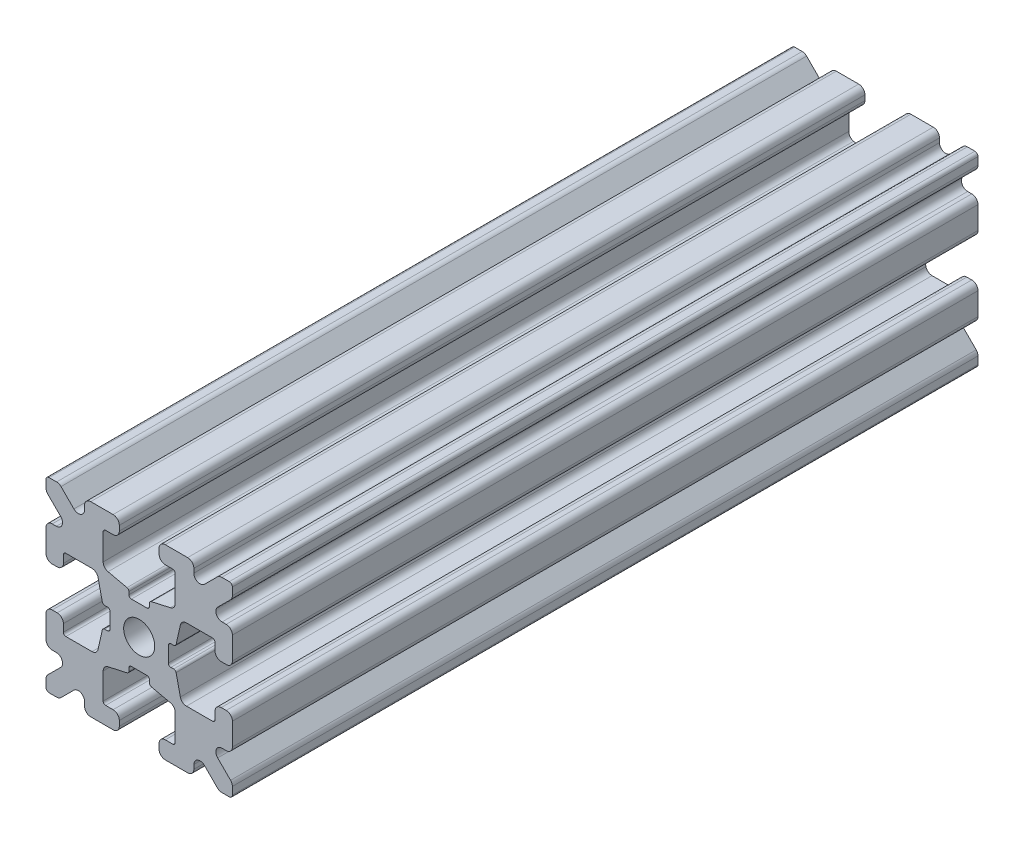
SolidWorks part; units mm, degrees
ref_plane "Front Plane" through (0, 0, 0) normal (0, 0, 1) x (1, 0, 0)
ref_plane "Top Plane" through (0, 0, 0) normal (0, 1, 0) x (1, 0, 0)
ref_plane "Right Plane" through (0, 0, 0) normal (1, 0, 0) x (0, 0, -1)
sketch "Profile" plane through (0, 0, 0) normal (0, 0, 1) x (1, 0, 0)
  line L0 (0.6255, -2.3471) -> (-0.6255, -2.3471)
  line L1 (-0.8255, -2.5471) -> (-0.8255, -2.7749)
  line L2 (-0.9818, -2.97) -> (-2.5094, -3.3124)
  line L3 (-2.9, -3.8003) -> (-2.9, -5.9)
  line L4 (-2.7, -6.1) -> (-2.1, -6.1)
  line L5 (-1.6, -6.6) -> (-1.6, -7)
  line L6 (-4.4, -7) -> (-4.4, -6.6678)
  line L7 (-5.2536, -6.3142) -> (-6.2929, -7.3536)
  line L8 (-7.3536, -6.2929) -> (-6.3142, -5.2536)
  line L9 (-6.6678, -4.4) -> (-7, -4.4)
  line L10 (-7.5, -2.1) -> (-7.5, -3.9)
  line L11 (-7, -1.6) -> (-6.6, -1.6)
  line L12 (-6.1, -2.1) -> (-6.1, -2.7)
  line L13 (-5.9, -2.9) -> (-3.8003, -2.9)
  line L14 (-3.3124, -2.5094) -> (-2.97, -0.9818)
  line L15 (-2.7749, -0.8255) -> (-2.5471, -0.8255)
  line L16 (-2.3471, -0.6255) -> (-2.3471, 0.6255)
  line L17 (-2.5471, 0.8255) -> (-2.7749, 0.8255)
  line L18 (-2.97, 0.9818) -> (-3.3124, 2.5094)
  line L19 (-3.8003, 2.9) -> (-5.9, 2.9)
  line L20 (-6.1, 2.7) -> (-6.1, 2.1)
  line L21 (-6.6, 1.6) -> (-7, 1.6)
  line L22 (-7, 4.4) -> (-6.6678, 4.4)
  line L23 (-6.3142, 5.2536) -> (-7.3536, 6.2929)
  line L24 (-6.2929, 7.3536) -> (-5.2536, 6.3142)
  line L25 (-4.4, 6.6678) -> (-4.4, 7)
  line L26 (-1.6, 7) -> (-1.6, 6.6)
  line L27 (-2.1, 6.1) -> (-2.7, 6.1)
  line L28 (-2.9, 5.9) -> (-2.9, 3.8003)
  line L29 (-2.5094, 3.3124) -> (-0.9818, 2.97)
  line L30 (-0.8255, 2.7749) -> (-0.8255, 2.5471)
  line L31 (-0.6255, 2.3471) -> (0.6255, 2.3471)
  line L32 (0.8255, 2.5471) -> (0.8255, 2.7749)
  line L33 (0.9818, 2.97) -> (2.5094, 3.3124)
  line L34 (2.9, 3.8003) -> (2.9, 5.9)
  line L35 (2.7, 6.1) -> (2.1, 6.1)
  line L36 (1.6, 6.6) -> (1.6, 7)
  line L37 (4.4, 7) -> (4.4, 6.6678)
  line L38 (5.2536, 6.3142) -> (6.2929, 7.3536)
  line L39 (7.25, 7.5) -> (6.6464, 7.5)
  line L40 (7.3536, 6.2929) -> (6.3142, 5.2536)
  line L41 (6.6678, 4.4) -> (7, 4.4)
  line L42 (7, 1.6) -> (6.6, 1.6)
  line L43 (6.1, 2.1) -> (6.1, 2.7)
  line L44 (5.9, 2.9) -> (3.8003, 2.9)
  line L45 (3.3124, 2.5094) -> (2.97, 0.9818)
  line L46 (2.7749, 0.8255) -> (2.5471, 0.8255)
  line L47 (2.3471, 0.6255) -> (2.3471, -0.6255)
  line L48 (2.5471, -0.8255) -> (2.7749, -0.8255)
  line L49 (2.97, -0.9818) -> (3.3124, -2.5094)
  line L50 (3.8003, -2.9) -> (5.9, -2.9)
  line L51 (6.1, -2.7) -> (6.1, -2.1)
  line L52 (6.6, -1.6) -> (7, -1.6)
  line L53 (7.5, -3.9) -> (7.5, -2.1)
  line L54 (7, -4.4) -> (6.6678, -4.4)
  line L55 (6.3142, -5.2536) -> (7.3536, -6.2929)
  line L56 (6.6464, -7.5) -> (7.25, -7.5)
  line L57 (6.2929, -7.3536) -> (5.2536, -6.3142)
  line L58 (4.4, -6.6678) -> (4.4, -7)
  line L59 (1.6, -7) -> (1.6, -6.6)
  line L60 (2.1, -6.1) -> (2.7, -6.1)
  line L61 (2.9, -5.9) -> (2.9, -3.8003)
  line L62 (2.5094, -3.3124) -> (0.9818, -2.97)
  line L63 (0.8255, -2.7749) -> (0.8255, -2.5471)
  line L64 (-7.5, 3.9) -> (-7.5, 2.1)
  line L65 (-6.6464, 7.5) -> (-7.25, 7.5)
  line L66 (-3.9, -7.5) -> (-2.1, -7.5)
  line L67 (7.5, 2.1) -> (7.5, 3.9)
  line L68 (-7.5, 7.25) -> (-7.5, 6.6464)
  line L69 (7.5, -7.25) -> (7.5, -6.6464)
  line L70 (7.5, 6.6464) -> (7.5, 7.25)
  line L71 (-2.1, 7.5) -> (-3.9, 7.5)
  line L72 (-7.5, -6.6464) -> (-7.5, -7.25)
  line L73 (3.9, 7.5) -> (2.1, 7.5)
  line L74 (2.1, -7.5) -> (3.9, -7.5)
  line L75 (-7.25, -7.5) -> (-6.6464, -7.5)
  circle A0 centre (0, 0) radius 1.25
  arc A1 (0.8255, -2.5471) -> (0.6255, -2.3471) centre (0.6255, -2.5471) ccw
  arc A2 (-0.6255, -2.3471) -> (-0.8255, -2.5471) centre (-0.6255, -2.5471) ccw
  arc A3 (-0.9818, -2.97) -> (-0.8255, -2.7749) centre (-1.0255, -2.7749) ccw
  arc A4 (-2.5094, -3.3124) -> (-2.9, -3.8003) centre (-2.4, -3.8003) ccw
  arc A5 (-2.9, -5.9) -> (-2.7, -6.1) centre (-2.7, -5.9) ccw
  arc A6 (-1.6, -6.6) -> (-2.1, -6.1) centre (-2.1, -6.6) ccw
  arc A7 (-2.1, -7.5) -> (-1.6, -7) centre (-2.1, -7) ccw
  arc A8 (-4.4, -7) -> (-3.9, -7.5) centre (-3.9, -7) ccw
  arc A9 (-4.4, -6.6678) -> (-5.2536, -6.3142) centre (-4.9, -6.6678) ccw
  arc A10 (-6.6464, -7.5) -> (-6.2929, -7.3536) centre (-6.6464, -7) ccw
  arc A11 (-7.5, -7.25) -> (-7.25, -7.5) centre (-7.25, -7.25) ccw
  arc A12 (-7.3536, -6.2929) -> (-7.5, -6.6464) centre (-7, -6.6464) ccw
  arc A13 (-6.3142, -5.2536) -> (-6.6678, -4.4) centre (-6.6678, -4.9) ccw
  arc A14 (-7.5, -3.9) -> (-7, -4.4) centre (-7, -3.9) ccw
  arc A15 (-7, -1.6) -> (-7.5, -2.1) centre (-7, -2.1) ccw
  arc A16 (-6.1, -2.1) -> (-6.6, -1.6) centre (-6.6, -2.1) ccw
  arc A17 (-6.1, -2.7) -> (-5.9, -2.9) centre (-5.9, -2.7) ccw
  arc A18 (-3.8003, -2.9) -> (-3.3124, -2.5094) centre (-3.8003, -2.4) ccw
  arc A19 (-2.7749, -0.8255) -> (-2.97, -0.9818) centre (-2.7749, -1.0255) ccw
  arc A20 (-2.5471, -0.8255) -> (-2.3471, -0.6255) centre (-2.5471, -0.6255) ccw
  arc A21 (-2.3471, 0.6255) -> (-2.5471, 0.8255) centre (-2.5471, 0.6255) ccw
  arc A22 (-2.97, 0.9818) -> (-2.7749, 0.8255) centre (-2.7749, 1.0255) ccw
  arc A23 (-3.3124, 2.5094) -> (-3.8003, 2.9) centre (-3.8003, 2.4) ccw
  arc A24 (-5.9, 2.9) -> (-6.1, 2.7) centre (-5.9, 2.7) ccw
  arc A25 (-6.6, 1.6) -> (-6.1, 2.1) centre (-6.6, 2.1) ccw
  arc A26 (-7.5, 2.1) -> (-7, 1.6) centre (-7, 2.1) ccw
  arc A27 (-7, 4.4) -> (-7.5, 3.9) centre (-7, 3.9) ccw
  arc A28 (-6.6678, 4.4) -> (-6.3142, 5.2536) centre (-6.6678, 4.9) ccw
  arc A29 (-7.5, 6.6464) -> (-7.3536, 6.2929) centre (-7, 6.6464) ccw
  arc A30 (-7.25, 7.5) -> (-7.5, 7.25) centre (-7.25, 7.25) ccw
  arc A31 (-6.2929, 7.3536) -> (-6.6464, 7.5) centre (-6.6464, 7) ccw
  arc A32 (-5.2536, 6.3142) -> (-4.4, 6.6678) centre (-4.9, 6.6678) ccw
  arc A33 (-3.9, 7.5) -> (-4.4, 7) centre (-3.9, 7) ccw
  arc A34 (-1.6, 7) -> (-2.1, 7.5) centre (-2.1, 7) ccw
  arc A35 (-2.1, 6.1) -> (-1.6, 6.6) centre (-2.1, 6.6) ccw
  arc A36 (-2.7, 6.1) -> (-2.9, 5.9) centre (-2.7, 5.9) ccw
  arc A37 (-2.9, 3.8003) -> (-2.5094, 3.3124) centre (-2.4, 3.8003) ccw
  arc A38 (-0.8255, 2.7749) -> (-0.9818, 2.97) centre (-1.0255, 2.7749) ccw
  arc A39 (-0.8255, 2.5471) -> (-0.6255, 2.3471) centre (-0.6255, 2.5471) ccw
  arc A40 (0.6255, 2.3471) -> (0.8255, 2.5471) centre (0.6255, 2.5471) ccw
  arc A41 (0.9818, 2.97) -> (0.8255, 2.7749) centre (1.0255, 2.7749) ccw
  arc A42 (2.5094, 3.3124) -> (2.9, 3.8003) centre (2.4, 3.8003) ccw
  arc A43 (2.9, 5.9) -> (2.7, 6.1) centre (2.7, 5.9) ccw
  arc A44 (1.6, 6.6) -> (2.1, 6.1) centre (2.1, 6.6) ccw
  arc A45 (2.1, 7.5) -> (1.6, 7) centre (2.1, 7) ccw
  arc A46 (4.4, 7) -> (3.9, 7.5) centre (3.9, 7) ccw
  arc A47 (4.4, 6.6678) -> (5.2536, 6.3142) centre (4.9, 6.6678) ccw
  arc A48 (6.6464, 7.5) -> (6.2929, 7.3536) centre (6.6464, 7) ccw
  arc A49 (7.5, 7.25) -> (7.25, 7.5) centre (7.25, 7.25) ccw
  arc A50 (7.3536, 6.2929) -> (7.5, 6.6464) centre (7, 6.6464) ccw
  arc A51 (6.3142, 5.2536) -> (6.6678, 4.4) centre (6.6678, 4.9) ccw
  arc A52 (7.5, 3.9) -> (7, 4.4) centre (7, 3.9) ccw
  arc A53 (7, 1.6) -> (7.5, 2.1) centre (7, 2.1) ccw
  arc A54 (6.1, 2.1) -> (6.6, 1.6) centre (6.6, 2.1) ccw
  arc A55 (6.1, 2.7) -> (5.9, 2.9) centre (5.9, 2.7) ccw
  arc A56 (3.8003, 2.9) -> (3.3124, 2.5094) centre (3.8003, 2.4) ccw
  arc A57 (2.7749, 0.8255) -> (2.97, 0.9818) centre (2.7749, 1.0255) ccw
  arc A58 (2.5471, 0.8255) -> (2.3471, 0.6255) centre (2.5471, 0.6255) ccw
  arc A59 (2.3471, -0.6255) -> (2.5471, -0.8255) centre (2.5471, -0.6255) ccw
  arc A60 (2.97, -0.9818) -> (2.7749, -0.8255) centre (2.7749, -1.0255) ccw
  arc A61 (3.3124, -2.5094) -> (3.8003, -2.9) centre (3.8003, -2.4) ccw
  arc A62 (5.9, -2.9) -> (6.1, -2.7) centre (5.9, -2.7) ccw
  arc A63 (6.6, -1.6) -> (6.1, -2.1) centre (6.6, -2.1) ccw
  arc A64 (7.5, -2.1) -> (7, -1.6) centre (7, -2.1) ccw
  arc A65 (7, -4.4) -> (7.5, -3.9) centre (7, -3.9) ccw
  arc A66 (6.6678, -4.4) -> (6.3142, -5.2536) centre (6.6678, -4.9) ccw
  arc A67 (7.5, -6.6464) -> (7.3536, -6.2929) centre (7, -6.6464) ccw
  arc A68 (7.25, -7.5) -> (7.5, -7.25) centre (7.25, -7.25) ccw
  arc A69 (6.2929, -7.3536) -> (6.6464, -7.5) centre (6.6464, -7) ccw
  arc A70 (5.2536, -6.3142) -> (4.4, -6.6678) centre (4.9, -6.6678) ccw
  arc A71 (3.9, -7.5) -> (4.4, -7) centre (3.9, -7) ccw
  arc A72 (1.6, -7) -> (2.1, -7.5) centre (2.1, -7) ccw
  arc A73 (2.1, -6.1) -> (1.6, -6.6) centre (2.1, -6.6) ccw
  arc A74 (2.7, -6.1) -> (2.9, -5.9) centre (2.7, -5.9) ccw
  arc A75 (2.9, -3.8003) -> (2.5094, -3.3124) centre (2.4, -3.8003) ccw
  arc A76 (0.8255, -2.7749) -> (0.9818, -2.97) centre (1.0255, -2.7749) ccw
extrude "Boss-Extrude1" add sketch "Profile" against normal blind 60
